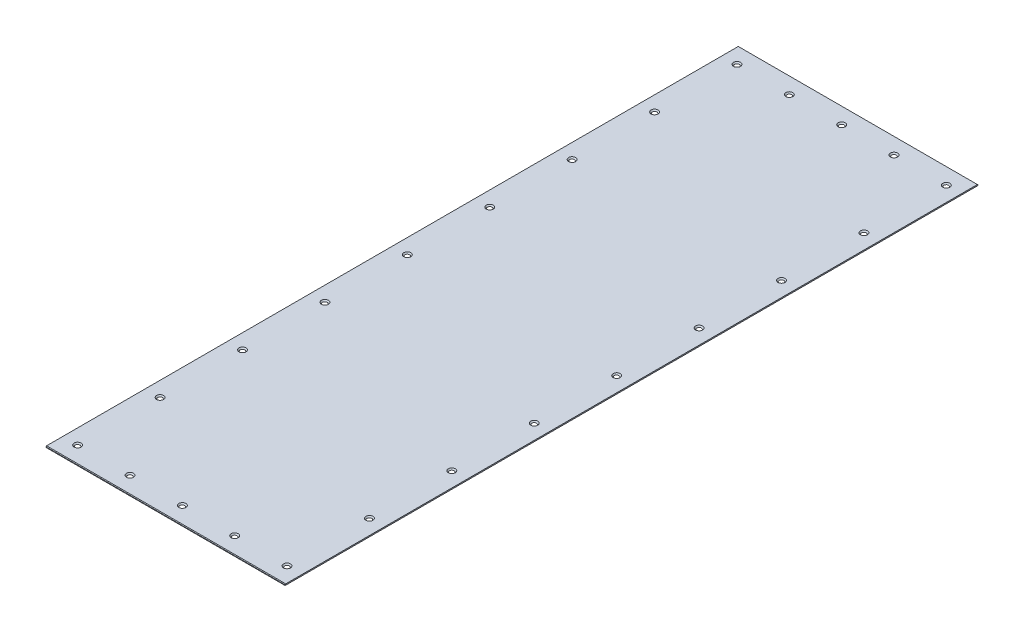
SolidWorks part; units mm, degrees
ref_plane "Front" through (0, 0, 0) normal (0, 0, 1) x (1, 0, 0)
ref_plane "Top" through (0, 0, 0) normal (0, 1, 0) x (1, 0, 0)
ref_plane "Right" through (0, 0, 0) normal (1, 0, 0) x (0, 0, -1)
sketch "Sketch1" plane through (0, 0, 0) normal (0, 1, 0) x (1, 0, 0)
  line L1 (-160.5, -465) -> (160.5, -465)
  line L2 (-160.5, -465) -> (-160.5, 465)
  line L3 (-160.5, 465) -> (160.5, 465)
  line L4 (160.5, -465) -> (160.5, 465)
  line L5 (-160.5, -465) -> (160.5, 465) construction
  line L6 (-160.5, 465) -> (160.5, -465) construction
  point P0 (0, 0)
  dimension "D1" = 321
  dimension "D2" = 930
extrude "Extrude1" add sketch "Sketch1" along normal blind 1.5875
chamfer "Chamfer1" distance 0.7937 angle 45 2 edges at (0, 1.5875, -465) (0, 1.5875, 465)
sketch "Sketch2" plane through (0, 1.5875, 0) normal (0, 1, 0) x (1, 0, 0)
  line L0 (-160.5, -465) -> (160.5, -465) construction
  line L1 (-160.5, -465) -> (160.5, -465)
  line L2 (160.5, 465) -> (-160.5, 465) construction
  line L3 (160.5, 465) -> (-160.5, 465)
  line L4 (-160.5, 464.2062) -> (-160.5, -464.2063) construction
  line L5 (160.5, -464.2063) -> (160.5, 464.2062) construction
  point P4 (-140.5, 442.5)
  point P5 (-70.25, 442.5)
  point P6 (0, 442.5)
  point P7 (70.25, 442.5)
  point P8 (140.5, 442.5)
  point P9 (140.5, 331.875)
  point P10 (140.5, 221.25)
  point P11 (140.5, 0)
  point P13 (140.5, -221.25)
  point P14 (140.5, -331.875)
  point P15 (140.5, -442.5)
  point P16 (140.5, 110.625)
  point P17 (140.5, -110.625)
  point P18 (-140.5, 331.875)
  point P19 (-140.5, 221.25)
  point P20 (-140.5, 110.625)
  point P21 (-140.5, 0)
  point P22 (-140.5, -110.625)
  point P23 (-140.5, -221.25)
  point P24 (-140.5, -331.875)
  point P25 (-140.5, -442.5)
  point P26 (-70.25, -442.5)
  point P27 (0, -442.5)
  point P28 (70.25, -442.5)
  dimension "D1" = 20
  dimension "D2" = 20
  dimension "D3" = 22.5
  dimension "D4" = 281
  dimension "D5" = 70.25
  dimension "D6" = 70.25
  dimension "D7" = 70.25
  dimension "D8" = 22.5
  dimension "D9" = 885
  dimension "D10" = 110.625
  dimension "D11" = 110.625
  dimension "D12" = 110.625
  dimension "D13" = 110.625
  dimension "D14" = 110.625
  dimension "D15" = 110.625
  dimension "D16" = 110.625
hole_wizard "CSK for M4 Flat Head Machine Screw1" positions "3DSketch1" profile "Sketch3" countersink size "M4" standard "Ansi Metric" end condition through all
sketch3d "3DSketch1"
  point P1 (-140.5, 1.5875, -442.5)
  point P4 (-70.25, 1.5875, -442.5)
  point P7 (0, 1.5875, -442.5)
  point P10 (70.25, 1.5875, -442.5)
  point P13 (140.5, 1.5875, -442.5)
  point P16 (-140.5, 1.5875, -331.875)
  point P19 (140.5, 1.5875, -331.875)
  point P22 (-140.5, 1.5875, -221.25)
  point P25 (140.5, 1.5875, -221.25)
  point P28 (-140.5, 1.5875, -110.625)
  point P31 (140.5, 1.5875, -110.625)
  point P34 (-140.5, 1.5875, 0)
  point P37 (140.5, 1.5875, 0)
  point P40 (-140.5, 1.5875, 110.625)
  point P43 (-140.5, 1.5875, 221.25)
  point P46 (-140.5, 1.5875, 331.875)
  point P49 (140.5, 1.5875, 110.625)
  point P52 (140.5, 1.5875, 221.25)
  point P55 (140.5, 1.5875, 331.875)
  point P58 (-140.5, 1.5875, 442.5)
  point P61 (-70.25, 1.5875, 442.5)
  point P64 (0, 1.5875, 442.5)
  point P67 (70.25, 1.5875, 442.5)
  point P70 (140.5, 1.5875, 442.5)
sketch "Sketch3" plane through (-140.5, 1.5875, -442.5) normal (1, 0, 0) x (0, 0, 1)
  line L0 (0, 0) -> (0, 1.5875)
  line L1 (0, 1.5875) -> (2.25, 1.5875)
  line L2 (2.25, 1.5875) -> (2.25, 2.45)
  line L3 (2.25, 2.45) -> (4.7, 0)
  line L5 (4.7, 0) -> (0, 0)
  line L6 (-2.25, 2.45) -> (-4.7, 0) construction
  line L11 (0, -6.35) -> (0, 107.95) construction
  dimension "Thru Hole Dia." = 4.5
  dimension "Thru Hole Depth" = 1.5875
  dimension "Near C'Sink Dia." = 9.4
  dimension "Near C'Sink Angle" = 90
equation "\"D5@Sketch2\" = \"D4@Sketch2\"/4"
equation "\"D6@Sketch2\" = \"D5@Sketch2\""
equation "\"D7@Sketch2\" = \"D6@Sketch2\""
equation "\"D10@Sketch2\" = \"D9@Sketch2\"/8"
equation "\"D11@Sketch2\" = \"D10@Sketch2\""
equation "\"D12@Sketch2\" = \"D11@Sketch2\""
equation "\"D13@Sketch2\" = \"D12@Sketch2\""
equation "\"D14@Sketch2\" = \"D13@Sketch2\""
equation "\"D15@Sketch2\" = \"D14@Sketch2\""
equation "\"D16@Sketch2\" = \"D15@Sketch2\""
